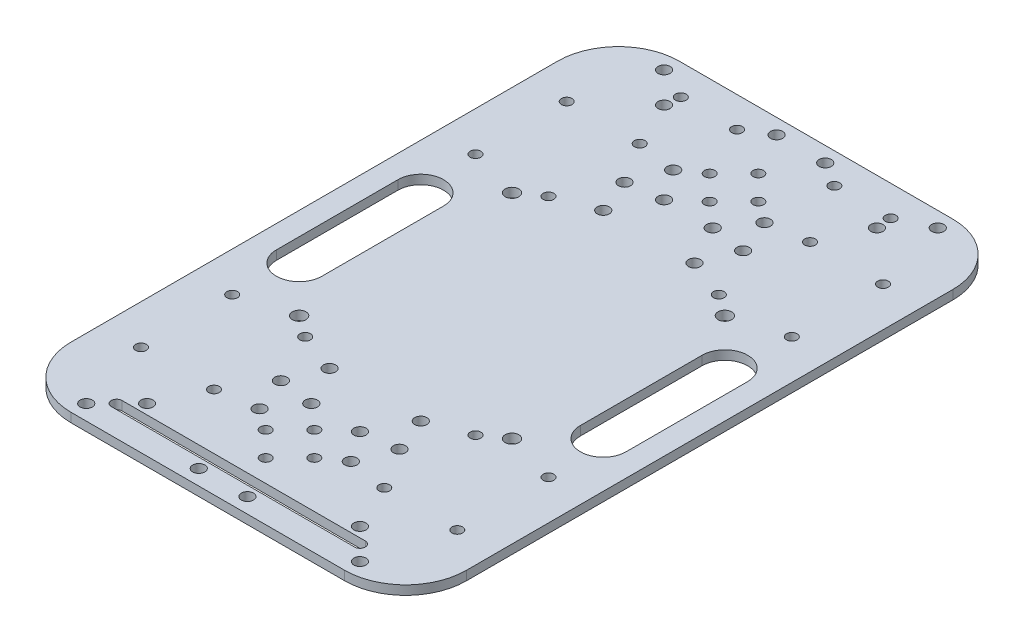
SolidWorks part; units mm, degrees
ref_plane "前视基准面" through (0, 0, 0) normal (0, 0, 1) x (1, 0, 0)
ref_plane "上视基准面" through (0, 0, 0) normal (0, 1, 0) x (1, 0, 0)
ref_plane "右视基准面" through (0, 0, 0) normal (1, 0, 0) x (0, 0, -1)
other "Configuration Table"
sketch "草图1" plane through (0, 0, 0) normal (0, 1, 0) x (1, 0, 0)
  line L0 (-40, -90) -> (40, -90) construction
  line L1 (-65, -100) -> (65, -100)
  line L2 (-65, -100) -> (-65, 100)
  line L3 (-65, 100) -> (65, 100)
  line L4 (65, -100) -> (65, 100)
  line L5 (-65, -100) -> (65, 100) construction
  line L6 (-65, 100) -> (65, -100) construction
  line L7 (-40, -88.25) -> (40, -88.25)
  line L8 (-40, -91.75) -> (40, -91.75)
  line L9 (50, -20) -> (50, 20) construction
  line L10 (42.5, -20) -> (42.5, 20)
  line L11 (57.5, -20) -> (57.5, 20)
  line L12 (-50, -20) -> (-50, 20) construction
  line L13 (-57.5, -20) -> (-57.5, 20)
  line L14 (-42.5, -20) -> (-42.5, 20)
  line L15 (0, 100) -> (0, -100) construction
  line L16 (-65, 0) -> (65, 0) construction
  circle A0 centre (52, -70) radius 1.75
  circle A1 centre (52, -40) radius 1.75
  circle A2 centre (28, -40) radius 1.75
  circle A3 centre (28, -70) radius 1.75
  circle A4 centre (52, 40) radius 1.75
  circle A5 centre (52, 70) radius 1.75
  circle A6 centre (28, 70) radius 1.75
  circle A7 centre (28, 40) radius 1.75
  circle A8 centre (-28, 40) radius 1.75
  circle A9 centre (-28, 70) radius 1.75
  circle A10 centre (-52, 70) radius 1.75
  circle A11 centre (-52, 40) radius 1.75
  circle A12 centre (-28, -70) radius 1.75
  circle A13 centre (-28, -40) radius 1.75
  circle A14 centre (-52, -40) radius 1.75
  circle A15 centre (-52, -70) radius 1.75
  circle A16 centre (35, -35) radius 2.25
  circle A17 centre (-35, -35) radius 2.25
  circle A18 centre (-35, 35) radius 2.25
  circle A19 centre (35, 35) radius 2.25
  circle A20 centre (16, 90) radius 1.75
  circle A21 centre (-16, 90) radius 1.75
  circle A22 centre (-34.5, 90) radius 1.75
  circle A25 centre (34.5, 90) radius 1.75
  circle A26 centre (-8, 73) radius 1.75
  circle A29 centre (0, 65) radius 1.75
  circle A31 centre (0, 81) radius 1.75
  circle A34 centre (8, 73) radius 1.75
  circle A35 centre (-8, -73) radius 1.75
  circle A36 centre (0, -81) radius 1.75
  circle A37 centre (0, -65) radius 1.75
  circle A38 centre (8, -73) radius 1.75
  arc A39 (-40, -88.25) -> (-40, -91.75) centre (-40, -90) ccw
  arc A40 (40, -91.75) -> (40, -88.25) centre (40, -90) ccw
  arc A41 (42.5, -20) -> (57.5, -20) centre (50, -20) ccw
  arc A42 (57.5, 20) -> (42.5, 20) centre (50, 20) ccw
  arc A43 (-57.5, -20) -> (-42.5, -20) centre (-50, -20) ccw
  arc A44 (-42.5, 20) -> (-57.5, 20) centre (-50, 20) ccw
  circle A45 centre (15, 45) radius 2
  circle A46 centre (-15, 45) radius 2
  circle A47 centre (-15, 68) radius 2
  circle A48 centre (15, 68) radius 2
  circle A53 centre (15, -68) radius 2
  circle A54 centre (-15, -68) radius 2
  circle A55 centre (-15, -45) radius 2
  circle A56 centre (15, -45) radius 2
  circle A57 centre (35, 85) radius 2
  circle A58 centre (-35, 85) radius 2
  circle A59 centre (35, -85) radius 2
  circle A60 centre (-35, -85) radius 2
  circle A61 centre (8, -58) radius 2
  circle A62 centre (8, -95) radius 2
  circle A63 centre (45, -95) radius 2
  circle A64 centre (-45, -95) radius 2
  circle A65 centre (-8, -95) radius 2
  circle A66 centre (-8, -58) radius 2
  circle A67 centre (45, 95) radius 2
  circle A68 centre (8, 95) radius 2
  circle A69 centre (-8, 95) radius 2
  circle A70 centre (-45, 95) radius 2
  circle A71 centre (8, 58) radius 2
  circle A72 centre (-8, 58) radius 2
  circle A73 centre (19.5, -56.5) radius 2
  circle A74 centre (-19.5, -56.5) radius 2
  circle A75 centre (-19.5, 56.5) radius 2
  circle A76 centre (19.5, 56.5) radius 2
  point P0 (0, 0)
  point P77 (0, -90)
  point P91 (50, 0)
  point P99 (-50, 0)
  dimension "D3" = 3.5
  dimension "D4" = 3.5
  dimension "D5" = 3.5
  dimension "D6" = 3.5
  dimension "D12" = 4.5
  dimension "D24" = 3.5
  dimension "D25" = 3.5
  dimension "D26" = 3.5
  dimension "D27" = 3.5
  dimension "D32" = 3.5
  dimension "D33" = 3.5
  dimension "D34" = 3.5
  dimension "D35" = 3.5
  dimension "D40" = 4.5
  dimension "D41" = 4.5
  dimension "D42" = 4.5
  dimension "D43" = 3.5
  dimension "D44" = 3.5
  dimension "D45" = 3.5
  dimension "D46" = 3.5
  dimension "D63" = 3.5
  dimension "D64" = 3.5
  dimension "D65" = 3.5
  dimension "D66" = 3.5
  dimension "D75" = 3.5
  dimension "D76" = 3.5
  dimension "D77" = 3.5
  dimension "D78" = 3.5
  dimension "D87" = 3.5
  dimension "D88" = 3.5
  dimension "D89" = 3.5
  dimension "D90" = 3.5
  dimension "D102" = 80
  dimension "D111" = 4
  dimension "D112" = 4
  dimension "D113" = 4
  dimension "D114" = 4
  dimension "D129" = 4
  dimension "D130" = 4
  dimension "D131" = 4
  dimension "D132" = 4
  dimension "D135" = 4
  dimension "D136" = 4
  dimension "D141" = 4
  dimension "D142" = 4
  dimension "D147" = 4
  dimension "D148" = 4
  dimension "D149" = 4
  dimension "D156" = 4
  dimension "D1" = 130
  dimension "D2" = 200
  dimension "D7" = 24
  dimension "D8" = 24
  dimension "D9" = 30
  dimension "D10" = 30
  dimension "D11" = 13
  dimension "D13" = 70
  dimension "D14" = 70
  dimension "D15" = 70
  dimension "D16" = 70
  dimension "D17" = 30
  dimension "D18" = 0
  dimension "D19" = 0
  dimension "D20" = 30
  dimension "D21" = 13
  dimension "D22" = 0
  dimension "D23" = 24
  dimension "D28" = 0
  dimension "D29" = 0
  dimension "D30" = 30
  dimension "D31" = 0
  dimension "D36" = 35
  dimension "D37" = 0
  dimension "D38" = 35
  dimension "D39" = 0
  dimension "D47" = 24
  dimension "D48" = 30
  dimension "D49" = 30
  dimension "D50" = 13
  dimension "D51" = 0
  dimension "D52" = 0
  dimension "D53" = 0
  dimension "D54" = 0
  dimension "D55" = 30
  dimension "D56" = 13
  dimension "D57" = 0
  dimension "D58" = 24
  dimension "D59" = 30
  dimension "D60" = 0
  dimension "D61" = 0
  dimension "D62" = 0
  dimension "D67" = 32
  dimension "D68" = 69
  dimension "D69" = 10
  dimension "D70" = 10
  dimension "D71" = 16
  dimension "D72" = 34.5
  dimension "D73" = 0
  dimension "D74" = 0
  dimension "D79" = 16
  dimension "D80" = 16
  dimension "D81" = 0
  dimension "D82" = 0
  dimension "D83" = 8
  dimension "D84" = 8
  dimension "D85" = 65
  dimension "D86" = 8
  dimension "D91" = 16
  dimension "D92" = 16
  dimension "D93" = 8
  dimension "D94" = 8
  dimension "D95" = 0
  dimension "D96" = 8
  dimension "D97" = 65
  dimension "D98" = 0
  dimension "D99" = 3.5
  dimension "D100" = 0
  dimension "D101" = 10
  dimension "D103" = 0
  dimension "D104" = 40
  dimension "D105" = 15
  dimension "D106" = 15
  dimension "D107" = 0
  dimension "D108" = 15
  dimension "D109" = 40
  dimension "D110" = 15
  dimension "D115" = 30
  dimension "D116" = 0
  dimension "D117" = 0
  dimension "D118" = 23
  dimension "D119" = 0
  dimension "D120" = 15
  dimension "D121" = 45
  dimension "D122" = 0
  dimension "D123" = 30
  dimension "D124" = 23
  dimension "D125" = 45
  dimension "D126" = 0
  dimension "D127" = 0
  dimension "D128" = 0
  dimension "D133" = 15
  dimension "D134" = 0
  dimension "D137" = 70
  dimension "D138" = 0
  dimension "D139" = 35
  dimension "D140" = 15
  dimension "D143" = 0
  dimension "D144" = 15
  dimension "D145" = 70
  dimension "D146" = 35
  dimension "D150" = 0
  dimension "D151" = 0
  dimension "D152" = 8
  dimension "D153" = 37
  dimension "D154" = 37
  dimension "D155" = 5
  dimension "D157" = 19.5
  dimension "D158" = 56.5
extrude "凸台-拉伸2" add sketch "草图1" along normal blind 3 contours L2 L1 L4 L3 | A11 | A18 | A8 | A10 | A9 | A22 | A21 | A20 | A25 | A6 | A31 | A26 | A34 | A29 | A5 | A4 | A7 | A19 | A1 | A16 | A2 | A0 | A3 | A37 | A35 | A38 | A36 | A13 | A17 | A14 | A15 | A12 | L7 A40 L8 A39 | A46 | A47 | A48 | A45 | A56 | A55 | A53 | A54 | A57 | A58 | A59 | A60 | A63 | A62 | A61 | A65 | A64 | A66 | A68 | A67 | A71 | A72 | A69 | A70 | L11 A41 L10 A42 | L13 A44 L14 A43 | A76 | A75 | A73 | A74
fillet "圆角1" radius 20 1 edges at (65, 1.5, 100)
fillet "圆角2" radius 20 1 edges at (-65, 1.5, 100)
fillet "圆角3" radius 20 1 edges at (-65, 1.5, -100)
fillet "圆角4" radius 20 1 edges at (65, 1.5, -100)
